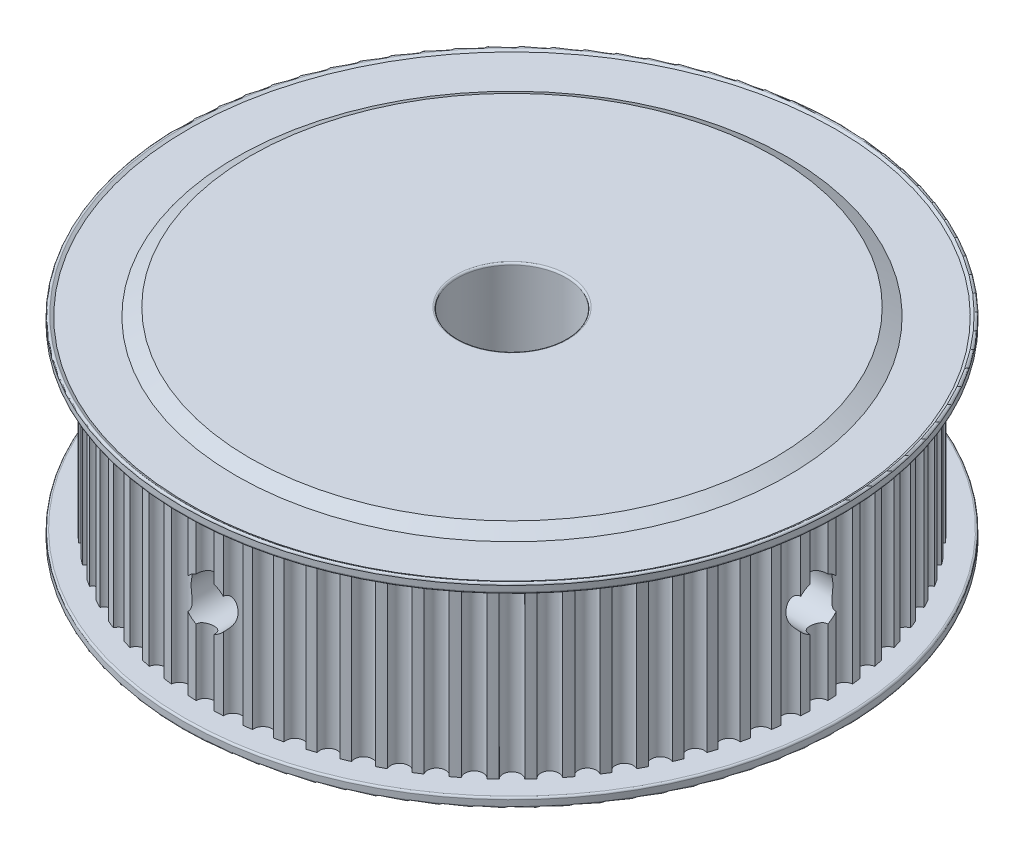
SolidWorks part; units mm, degrees
material "1060 Alloy"
ref_plane "Front Plane" through (0, 0, 0) normal (0, 0, 1) x (1, 0, 0)
ref_plane "Top Plane" through (0, 0, 0) normal (0, 1, 0) x (1, 0, 0)
ref_plane "Right Plane" through (0, 0, 0) normal (1, 0, 0) x (0, 0, -1)
sketch "Sketch1" plane through (0, 0, 0) normal (0, 0, 1) x (1, 0, 0)
  line L0 (0, 0) -> (0, 23) construction
  line L1 (0, 0) -> (0, 1.75)
  line L2 (0, 1.75) -> (36.5, 1.75)
  line L3 (36.5, 1.75) -> (36.5, 0.55)
  line L4 (36.5, 0.55) -> (35.8938, 0.9)
  line L5 (35.8938, 0.9) -> (30.5588, 0.9)
  line L6 (30.5588, 0.9) -> (29, 0)
  line L7 (29, 0) -> (0, 0)
  dimension "D1" = 23
  dimension "D3" = 36.5
  dimension "D4" = 29
  dimension "D5" = 150
  dimension "D6" = 150
  dimension "D7" = 1.75
  dimension "D8" = 1.2
  dimension "D9" = 0.85
revolve "Revolve1" add sketch "Sketch1" angle 360 about L0
fillet "Fillet1" radius 0.2 2 edges at (0, 0.55, -36.5) (0, 1.75, -36.5)
sketch "Sketch2" plane through (0, 1.75, 0) normal (0, 1, 0) x (1, 0, 0)
  arc A0 (1.9659, 33.9431) -> (0.9999, 33.9853) centre (0, 0) ccw
  circle A1 centre (0, 0) radius 33 construction
  arc A2 (-0.9999, 33.9853) -> (0.9999, 33.9853) centre (0, 34) ccw
  arc A3 (4.9168, 33.6426) -> (3.9581, 33.7688) centre (0, 0) ccw
  arc A4 (1.9659, 33.9431) -> (3.9581, 33.7688) centre (2.9633, 33.8706) ccw
  arc A5 (7.8302, 33.0861) -> (6.8862, 33.2954) centre (0, 0) ccw
  arc A6 (4.9168, 33.6426) -> (6.8862, 33.2954) centre (5.904, 33.4835) ccw
  arc A7 (10.6841, 32.2777) -> (9.7619, 32.5685) centre (0, 0) ccw
  arc A8 (7.8302, 33.0861) -> (9.7619, 32.5685) centre (8.7998, 32.8415) ccw
  arc A9 (13.4566, 31.2237) -> (12.5632, 31.5937) centre (0, 0) ccw
  arc A10 (10.6841, 32.2777) -> (12.5632, 31.5937) centre (11.6287, 31.9495) ccw
  arc A11 (16.1267, 29.9321) -> (15.269, 30.3786) centre (0, 0) ccw
  arc A12 (13.4566, 31.2237) -> (15.269, 30.3786) centre (14.369, 30.8145) ccw
  arc A13 (18.6741, 28.4126) -> (17.8586, 28.9322) centre (0, 0) ccw
  arc A14 (16.1267, 29.9321) -> (17.8586, 28.9322) centre (17, 29.4449) ccw
  arc A15 (21.0794, 26.677) -> (20.3122, 27.2656) centre (0, 0) ccw
  arc A16 (18.6741, 28.4126) -> (20.3122, 27.2656) centre (19.5016, 27.8512) ccw
  arc A17 (23.3242, 24.7383) -> (22.6113, 25.3915) centre (0, 0) ccw
  arc A18 (21.0794, 26.677) -> (22.6113, 25.3915) centre (21.8548, 26.0455) ccw
  arc A19 (25.3915, 22.6113) -> (24.7383, 23.3242) centre (0, 0) ccw
  arc A20 (23.3242, 24.7383) -> (24.7383, 23.3242) centre (24.0416, 24.0416) ccw
  arc A21 (27.2656, 20.3122) -> (26.677, 21.0794) centre (0, 0) ccw
  arc A22 (25.3915, 22.6113) -> (26.677, 21.0794) centre (26.0455, 21.8548) ccw
  arc A23 (28.9322, 17.8586) -> (28.4126, 18.6741) centre (0, 0) ccw
  arc A24 (27.2656, 20.3122) -> (28.4126, 18.6741) centre (27.8512, 19.5016) ccw
  arc A25 (30.3786, 15.269) -> (29.9321, 16.1267) centre (0, 0) ccw
  arc A26 (28.9322, 17.8586) -> (29.9321, 16.1267) centre (29.4449, 17) ccw
  arc A27 (31.5937, 12.5632) -> (31.2237, 13.4566) centre (0, 0) ccw
  arc A28 (30.3786, 15.269) -> (31.2237, 13.4566) centre (30.8145, 14.369) ccw
  arc A29 (32.5685, 9.7619) -> (32.2777, 10.6841) centre (0, 0) ccw
  arc A30 (31.5937, 12.5632) -> (32.2777, 10.6841) centre (31.9495, 11.6287) ccw
  arc A31 (33.2954, 6.8862) -> (33.0861, 7.8302) centre (0, 0) ccw
  arc A32 (32.5685, 9.7619) -> (33.0861, 7.8302) centre (32.8415, 8.7998) ccw
  arc A33 (33.7688, 3.9581) -> (33.6426, 4.9168) centre (0, 0) ccw
  arc A34 (33.2954, 6.8862) -> (33.6426, 4.9168) centre (33.4835, 5.904) ccw
  arc A35 (33.9853, 0.9999) -> (33.9431, 1.9659) centre (0, 0) ccw
  arc A36 (33.7688, 3.9581) -> (33.9431, 1.9659) centre (33.8706, 2.9633) ccw
  arc A37 (33.9431, -1.9659) -> (33.9853, -0.9999) centre (0, 0) ccw
  arc A38 (33.9853, 0.9999) -> (33.9853, -0.9999) centre (34, 0) ccw
  arc A39 (33.6426, -4.9168) -> (33.7688, -3.9581) centre (0, 0) ccw
  arc A40 (33.9431, -1.9659) -> (33.7688, -3.9581) centre (33.8706, -2.9633) ccw
  arc A41 (33.0861, -7.8302) -> (33.2954, -6.8862) centre (0, 0) ccw
  arc A42 (33.6426, -4.9168) -> (33.2954, -6.8862) centre (33.4835, -5.904) ccw
  arc A43 (32.2777, -10.6841) -> (32.5685, -9.7619) centre (0, 0) ccw
  arc A44 (33.0861, -7.8302) -> (32.5685, -9.7619) centre (32.8415, -8.7998) ccw
  arc A45 (31.2237, -13.4566) -> (31.5937, -12.5632) centre (0, 0) ccw
  arc A46 (32.2777, -10.6841) -> (31.5937, -12.5632) centre (31.9495, -11.6287) ccw
  arc A47 (29.9321, -16.1267) -> (30.3786, -15.269) centre (0, 0) ccw
  arc A48 (31.2237, -13.4566) -> (30.3786, -15.269) centre (30.8145, -14.369) ccw
  arc A49 (28.4126, -18.6741) -> (28.9322, -17.8586) centre (0, 0) ccw
  arc A50 (29.9321, -16.1267) -> (28.9322, -17.8586) centre (29.4449, -17) ccw
  arc A51 (26.677, -21.0794) -> (27.2656, -20.3122) centre (0, 0) ccw
  arc A52 (28.4126, -18.6741) -> (27.2656, -20.3122) centre (27.8512, -19.5016) ccw
  arc A53 (24.7383, -23.3242) -> (25.3915, -22.6113) centre (0, 0) ccw
  arc A54 (26.677, -21.0794) -> (25.3915, -22.6113) centre (26.0455, -21.8548) ccw
  arc A55 (22.6113, -25.3915) -> (23.3242, -24.7383) centre (0, 0) ccw
  arc A56 (24.7383, -23.3242) -> (23.3242, -24.7383) centre (24.0416, -24.0416) ccw
  arc A57 (20.3122, -27.2656) -> (21.0794, -26.677) centre (0, 0) ccw
  arc A58 (22.6113, -25.3915) -> (21.0794, -26.677) centre (21.8548, -26.0455) ccw
  arc A59 (17.8586, -28.9322) -> (18.6741, -28.4126) centre (0, 0) ccw
  arc A60 (20.3122, -27.2656) -> (18.6741, -28.4126) centre (19.5016, -27.8512) ccw
  arc A61 (15.269, -30.3786) -> (16.1267, -29.9321) centre (0, 0) ccw
  arc A62 (17.8586, -28.9322) -> (16.1267, -29.9321) centre (17, -29.4449) ccw
  arc A63 (12.5632, -31.5937) -> (13.4566, -31.2237) centre (0, 0) ccw
  arc A64 (15.269, -30.3786) -> (13.4566, -31.2237) centre (14.369, -30.8145) ccw
  arc A65 (9.7619, -32.5685) -> (10.6841, -32.2777) centre (0, 0) ccw
  arc A66 (12.5632, -31.5937) -> (10.6841, -32.2777) centre (11.6287, -31.9495) ccw
  arc A67 (6.8862, -33.2954) -> (7.8302, -33.0861) centre (0, 0) ccw
  arc A68 (9.7619, -32.5685) -> (7.8302, -33.0861) centre (8.7998, -32.8415) ccw
  arc A69 (3.9581, -33.7688) -> (4.9168, -33.6426) centre (0, 0) ccw
  arc A70 (6.8862, -33.2954) -> (4.9168, -33.6426) centre (5.904, -33.4835) ccw
  arc A71 (0.9999, -33.9853) -> (1.9659, -33.9431) centre (0, 0) ccw
  arc A72 (3.9581, -33.7688) -> (1.9659, -33.9431) centre (2.9633, -33.8706) ccw
  arc A73 (-1.9659, -33.9431) -> (-0.9999, -33.9853) centre (0, 0) ccw
  arc A74 (0.9999, -33.9853) -> (-0.9999, -33.9853) centre (0, -34) ccw
  arc A75 (-4.9168, -33.6426) -> (-3.9581, -33.7688) centre (0, 0) ccw
  arc A76 (-1.9659, -33.9431) -> (-3.9581, -33.7688) centre (-2.9633, -33.8706) ccw
  arc A77 (-7.8302, -33.0861) -> (-6.8862, -33.2954) centre (0, 0) ccw
  arc A78 (-4.9168, -33.6426) -> (-6.8862, -33.2954) centre (-5.904, -33.4835) ccw
  arc A79 (-10.6841, -32.2777) -> (-9.7619, -32.5685) centre (0, 0) ccw
  arc A80 (-7.8302, -33.0861) -> (-9.7619, -32.5685) centre (-8.7998, -32.8415) ccw
  arc A81 (-13.4566, -31.2237) -> (-12.5632, -31.5937) centre (0, 0) ccw
  arc A82 (-10.6841, -32.2777) -> (-12.5632, -31.5937) centre (-11.6287, -31.9495) ccw
  arc A83 (-16.1267, -29.9321) -> (-15.269, -30.3786) centre (0, 0) ccw
  arc A84 (-13.4566, -31.2237) -> (-15.269, -30.3786) centre (-14.369, -30.8145) ccw
  arc A85 (-18.6741, -28.4126) -> (-17.8586, -28.9322) centre (0, 0) ccw
  arc A86 (-16.1267, -29.9321) -> (-17.8586, -28.9322) centre (-17, -29.4449) ccw
  arc A87 (-21.0794, -26.677) -> (-20.3122, -27.2656) centre (0, 0) ccw
  arc A88 (-18.6741, -28.4126) -> (-20.3122, -27.2656) centre (-19.5016, -27.8512) ccw
  arc A89 (-23.3242, -24.7383) -> (-22.6113, -25.3915) centre (0, 0) ccw
  arc A90 (-21.0794, -26.677) -> (-22.6113, -25.3915) centre (-21.8548, -26.0455) ccw
  arc A91 (-25.3915, -22.6113) -> (-24.7383, -23.3242) centre (0, 0) ccw
  arc A92 (-23.3242, -24.7383) -> (-24.7383, -23.3242) centre (-24.0416, -24.0416) ccw
  arc A93 (-27.2656, -20.3122) -> (-26.677, -21.0794) centre (0, 0) ccw
  arc A94 (-25.3915, -22.6113) -> (-26.677, -21.0794) centre (-26.0455, -21.8548) ccw
  arc A95 (-28.9322, -17.8586) -> (-28.4126, -18.6741) centre (0, 0) ccw
  arc A96 (-27.2656, -20.3122) -> (-28.4126, -18.6741) centre (-27.8512, -19.5016) ccw
  arc A97 (-30.3786, -15.269) -> (-29.9321, -16.1267) centre (0, 0) ccw
  arc A98 (-28.9322, -17.8586) -> (-29.9321, -16.1267) centre (-29.4449, -17) ccw
  arc A99 (-31.5937, -12.5632) -> (-31.2237, -13.4566) centre (0, 0) ccw
  arc A100 (-30.3786, -15.269) -> (-31.2237, -13.4566) centre (-30.8145, -14.369) ccw
  arc A101 (-32.5685, -9.7619) -> (-32.2777, -10.6841) centre (0, 0) ccw
  arc A102 (-31.5937, -12.5632) -> (-32.2777, -10.6841) centre (-31.9495, -11.6287) ccw
  arc A103 (-33.2954, -6.8862) -> (-33.0861, -7.8302) centre (0, 0) ccw
  arc A104 (-32.5685, -9.7619) -> (-33.0861, -7.8302) centre (-32.8415, -8.7998) ccw
  arc A105 (-33.7688, -3.9581) -> (-33.6426, -4.9168) centre (0, 0) ccw
  arc A106 (-33.2954, -6.8862) -> (-33.6426, -4.9168) centre (-33.4835, -5.904) ccw
  arc A107 (-33.9853, -0.9999) -> (-33.9431, -1.9659) centre (0, 0) ccw
  arc A108 (-33.7688, -3.9581) -> (-33.9431, -1.9659) centre (-33.8706, -2.9633) ccw
  arc A109 (-33.9431, 1.9659) -> (-33.9853, 0.9999) centre (0, 0) ccw
  arc A110 (-33.9853, -0.9999) -> (-33.9853, 0.9999) centre (-34, 0) ccw
  arc A111 (-33.6426, 4.9168) -> (-33.7688, 3.9581) centre (0, 0) ccw
  arc A112 (-33.9431, 1.9659) -> (-33.7688, 3.9581) centre (-33.8706, 2.9633) ccw
  arc A113 (-33.0861, 7.8302) -> (-33.2954, 6.8862) centre (0, 0) ccw
  arc A114 (-33.6426, 4.9168) -> (-33.2954, 6.8862) centre (-33.4835, 5.904) ccw
  arc A115 (-32.2777, 10.6841) -> (-32.5685, 9.7619) centre (0, 0) ccw
  arc A116 (-33.0861, 7.8302) -> (-32.5685, 9.7619) centre (-32.8415, 8.7998) ccw
  arc A117 (-31.2237, 13.4566) -> (-31.5937, 12.5632) centre (0, 0) ccw
  arc A118 (-32.2777, 10.6841) -> (-31.5937, 12.5632) centre (-31.9495, 11.6287) ccw
  arc A119 (-29.9321, 16.1267) -> (-30.3786, 15.269) centre (0, 0) ccw
  arc A120 (-31.2237, 13.4566) -> (-30.3786, 15.269) centre (-30.8145, 14.369) ccw
  arc A121 (-28.4126, 18.6741) -> (-28.9322, 17.8586) centre (0, 0) ccw
  arc A122 (-29.9321, 16.1267) -> (-28.9322, 17.8586) centre (-29.4449, 17) ccw
  arc A123 (-26.677, 21.0794) -> (-27.2656, 20.3122) centre (0, 0) ccw
  arc A124 (-28.4126, 18.6741) -> (-27.2656, 20.3122) centre (-27.8512, 19.5016) ccw
  arc A125 (-24.7383, 23.3242) -> (-25.3915, 22.6113) centre (0, 0) ccw
  arc A126 (-26.677, 21.0794) -> (-25.3915, 22.6113) centre (-26.0455, 21.8548) ccw
  arc A127 (-22.6113, 25.3915) -> (-23.3242, 24.7383) centre (0, 0) ccw
  arc A128 (-24.7383, 23.3242) -> (-23.3242, 24.7383) centre (-24.0416, 24.0416) ccw
  arc A129 (-20.3122, 27.2656) -> (-21.0794, 26.677) centre (0, 0) ccw
  arc A130 (-22.6113, 25.3915) -> (-21.0794, 26.677) centre (-21.8548, 26.0455) ccw
  arc A131 (-17.8586, 28.9322) -> (-18.6741, 28.4126) centre (0, 0) ccw
  arc A132 (-20.3122, 27.2656) -> (-18.6741, 28.4126) centre (-19.5016, 27.8512) ccw
  arc A133 (-15.269, 30.3786) -> (-16.1267, 29.9321) centre (0, 0) ccw
  arc A134 (-17.8586, 28.9322) -> (-16.1267, 29.9321) centre (-17, 29.4449) ccw
  arc A135 (-12.5632, 31.5937) -> (-13.4566, 31.2237) centre (0, 0) ccw
  arc A136 (-15.269, 30.3786) -> (-13.4566, 31.2237) centre (-14.369, 30.8145) ccw
  arc A137 (-9.7619, 32.5685) -> (-10.6841, 32.2777) centre (0, 0) ccw
  arc A138 (-12.5632, 31.5937) -> (-10.6841, 32.2777) centre (-11.6287, 31.9495) ccw
  arc A139 (-6.8862, 33.2954) -> (-7.8302, 33.0861) centre (0, 0) ccw
  arc A140 (-9.7619, 32.5685) -> (-7.8302, 33.0861) centre (-8.7998, 32.8415) ccw
  arc A141 (-3.9581, 33.7688) -> (-4.9168, 33.6426) centre (0, 0) ccw
  arc A142 (-6.8862, 33.2954) -> (-4.9168, 33.6426) centre (-5.904, 33.4835) ccw
  arc A143 (-0.9999, 33.9853) -> (-1.9659, 33.9431) centre (0, 0) ccw
  arc A144 (-3.9581, 33.7688) -> (-1.9659, 33.9431) centre (-2.9633, 33.8706) ccw
  dimension "D1" = 68
  dimension "D2" = 66
  dimension "D3" = 72
extrude "Boss-Extrude1" add sketch "Sketch2" along normal blind 19.5
ref_plane "Plane1" through (0, 11.5, 0) normal (0, 1, 0) x (1, 0, 0)
mirror "Mirror1" about plane through (0, 11.5, 0) normal (0, 1, 0) of "Fillet1", "Revolve1"
sketch "Sketch4" plane through (0, 0, 0) normal (0, 0, 1) x (1, 0, 0)
  line L0 (-0.9999, 21.25) -> (-0.9999, 1.75) construction
  circle A0 centre (0, 11.5) radius 2.6
  point P5 (-0.9999, 11.5)
  dimension "D1" = 5.2
extrude "Cut-Extrude1" cut sketch "Sketch4" along normal blind 36.5
sketch "Sketch5" plane through (0, 0, 0) normal (1, 0, 0) x (0, 0, -1)
  line L1 (-0.9999, 21.25) -> (-0.9999, 1.75) construction
  circle A0 centre (0, 11.5) radius 2.6
  point P5 (-0.9999, 11.5)
  dimension "D1" = 5.2
extrude "Cut-Extrude2" cut sketch "Sketch5" along normal blind 36.5
sketch "Sketch3" plane through (0, 23, 0) normal (0, 1, 0) x (1, 0, 0)
  circle A0 centre (0, 0) radius 6
  dimension "D1" = 12
extrude "Cut-Extrude3" cut sketch "Sketch3" against normal through all
fillet "Fillet2" radius 0.2 2 edges at (0, 0, 6) (0, 23, 6)
scale "Scale2" scale about centroid uniform scaling yes scale factor 0.2
scale "Scale4" scale about centroid uniform scaling yes scale factor 2
